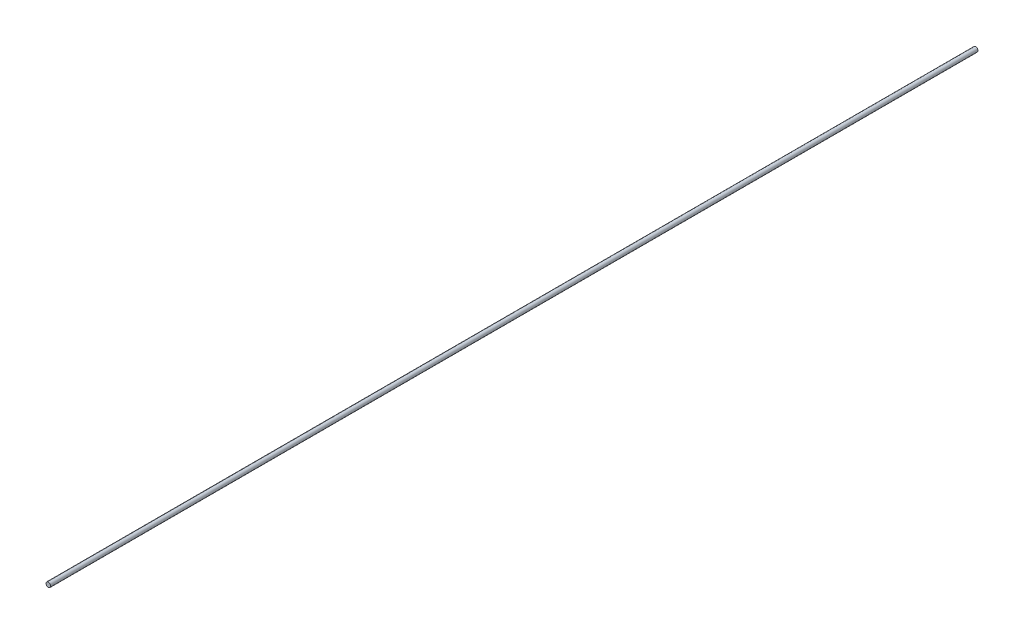
SolidWorks part; units mm, degrees
ref_plane "Plan de face" through (0, 0, 0) normal (0, 0, 1) x (1, 0, 0)
ref_plane "Plan de dessus" through (0, 0, 0) normal (0, 1, 0) x (1, 0, 0)
ref_plane "Plan de droite" through (0, 0, 0) normal (1, 0, 0) x (0, 0, -1)
sketch "Esquisse1" plane through (0, 0, 0) normal (0, 0, 1) x (1, 0, 0)
  circle A0 centre (0, 0) radius 2
  dimension "D1" = 4
extrude "Boss.-Extru.1" add sketch "Esquisse1" along normal blind 800
